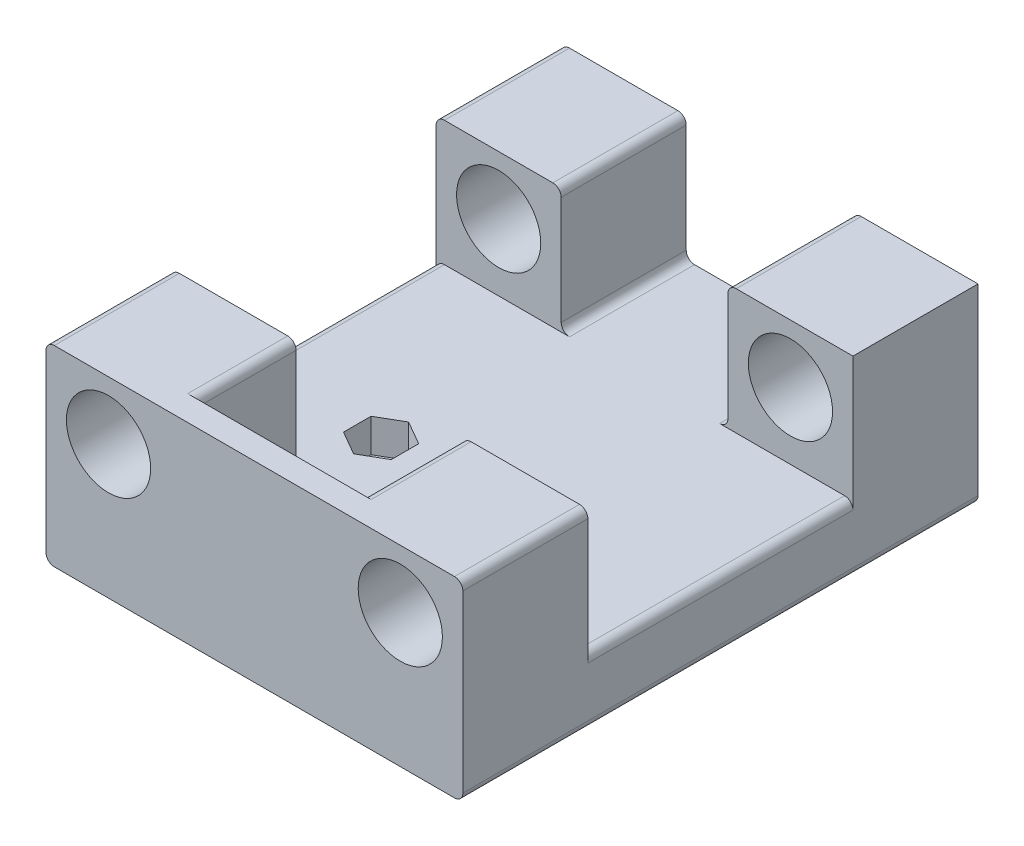
SolidWorks part; units mm, degrees
ref_plane "Front Plane" through (0, 0, 0) normal (0, 0, 1) x (1, 0, 0)
ref_plane "Top Plane" through (0, 0, 0) normal (0, 1, 0) x (1, 0, 0)
ref_plane "Right Plane" through (0, 0, 0) normal (1, 0, 0) x (0, 0, -1)
sketch "Sketch1" plane through (0, 0, 0) normal (0, 1, 0) x (1, 0, 0)
  line L1 (25, 30.9) -> (-25, 30.9)
  line L2 (25, 30.9) -> (25, -30.9)
  line L3 (25, -30.9) -> (-25, -30.9)
  line L4 (-25, 30.9) -> (-25, -30.9)
  line L5 (25, 30.9) -> (-25, -30.9) construction
  line L6 (25, -30.9) -> (-25, 30.9) construction
  point P0 (0, 0)
  dimension "D1" = 50
  dimension "D2" = 61.8
extrude "Boss-Extrude1" add sketch "Sketch1" along normal blind 5
sketch "Sketch2" plane through (0, 5, 0) normal (0, 1, 0) x (1, 0, 0)
  line L0 (-25, 30.9) -> (-25, -30.9) construction
  line L1 (-25, 30.9) -> (-10, 30.9)
  line L2 (-25, 30.9) -> (-25, 15.9)
  line L3 (-25, 15.9) -> (-10, 15.9)
  line L4 (-10, 30.9) -> (-10, 15.9)
  line L5 (25, -30.9) -> (25, 30.9) construction
  line L6 (25, 30.9) -> (10, 30.9)
  line L7 (25, 30.9) -> (25, 15.9)
  line L8 (25, 15.9) -> (10, 15.9)
  line L9 (10, 30.9) -> (10, 15.9)
  line L10 (25, 30.9) -> (-25, 30.9) construction
  line L11 (-25, -15.9) -> (-10, -15.9)
  line L12 (-25, -15.9) -> (-25, -30.9)
  line L13 (-25, -30.9) -> (-10, -30.9)
  line L14 (-10, -15.9) -> (-10, -30.9)
  line L15 (25, -15.9) -> (10, -15.9)
  line L16 (25, -15.9) -> (25, -30.9)
  line L17 (25, -30.9) -> (10, -30.9)
  line L18 (10, -15.9) -> (10, -30.9)
  line L19 (-25, -30.9) -> (25, -30.9) construction
  dimension "D1" = 15
  dimension "D2" = 15
extrude "Boss-Extrude2" add sketch "Sketch2" along normal blind 15
sketch "Sketch3" plane through (0, 0, 30.9) normal (0, 0, 1) x (1, 0, 0)
  line L0 (-25, 13) -> (25, 13) construction
  line L2 (25, 20) -> (25, 0) construction
  line L3 (-25, 20) -> (-25, 0) construction
  line L4 (-10, 5) -> (10, 5) construction
  line L5 (-17.5, 20) -> (-17.5, 0) construction
  line L6 (-25, 20) -> (-10, 20) construction
  line L7 (-25, 0) -> (25, 0) construction
  line L8 (17.5, 20) -> (17.5, 0) construction
  line L9 (10, 20) -> (25, 20) construction
  circle A0 centre (-17.5, 13) radius 5.05
  circle A1 centre (17.5, 13) radius 5.05
  point P3 (0, 13)
  point P19 (-17.5, 13)
  point P20 (17.5, 13)
  dimension "D2" = 10.1
  dimension "D3" = 10.1
  dimension "D1" = 8
extrude "Cut-Extrude1" cut sketch "Sketch3" against normal through all both and the other way through all
sketch "Sketch4" plane through (0, 5, 0) normal (0, 1, 0) x (1, 0, 0)
  line L0 (10, -15.9) -> (10, -30.9) construction
  line L1 (-10, -30.9) -> (10, -30.9)
  line L2 (-10, -30.9) -> (-10, -27.9)
  line L3 (-10, -27.9) -> (10, -27.9)
  line L4 (10, -30.9) -> (10, -27.9)
  dimension "D1" = 3
extrude "Boss-Extrude3" add sketch "Sketch4" along normal up to surface (15 mm away) up to face at (-17.5, 20, 23.4)
sketch "Sketch6" plane through (0, 0, 0) normal (0, -1, 0) x (1, 0, 0)
  line L4 (-25, 30.9) -> (-25, -30.9)
  line L5 (-25, -30.9) -> (25, -30.9)
  line L6 (25, -30.9) -> (25, 30.9)
  line L7 (25, 30.9) -> (-25, 30.9)
  line L8 (-25, 30.9) -> (-25, -30.9)
  line L9 (-25, -30.9) -> (25, -30.9)
  line L10 (25, -30.9) -> (25, 30.9)
  line L11 (25, 30.9) -> (-25, 30.9)
  dimension "D1" = 0
extrude "Boss-Extrude5" add sketch "Sketch6" along normal blind 3
fillet "Fillet1" radius 1 15 edges at (10, 20, -23.4) (10, 5, -23.4) (-10, 20, -23.4) (-10, 5, -23.4) (-10, 5, 21.9) (10, 5, 21.9) (10, 20, 21.9) (25, 20, 23.4) (-10, 20, 21.9) (-25, 20, 23.4) (-25, 20, -23.4) (25, 5, 0) (-25, 5, 0) (25, -3, 0) (-25, -3, 0)
sketch "Sketch7" plane through (0, 5, 0) normal (0, 1, 0) x (1, 0, 0)
  line L0 (-25, -5.9) -> (25, -5.9) construction
  line L1 (-25, -30.9) -> (-25, -15.9) construction
  line L2 (25, -15.9) -> (25, -30.9) construction
  line L3 (-9.8, -5.9) -> (9.8, -5.9) construction
  line L4 (-9, -15.9) -> (-9, -27.9) construction
  line L5 (-12.6579, -4.25) -> (-12.6579, -7.55)
  line L6 (-12.6579, -7.55) -> (-9.8, -9.2)
  line L7 (-9.8, -9.2) -> (-6.9421, -7.55)
  line L8 (-6.9421, -7.55) -> (-6.9421, -4.25)
  line L9 (-6.9421, -4.25) -> (-9.8, -2.6)
  line L10 (-9.8, -2.6) -> (-12.6579, -4.25)
  line L11 (-24, -30.9) -> (24, -30.9) construction
  line L12 (12.6579, -7.55) -> (12.6579, -4.25)
  line L13 (12.6579, -4.25) -> (9.8, -2.6)
  line L14 (9.8, -2.6) -> (6.9421, -4.25)
  line L15 (6.9421, -4.25) -> (6.9421, -7.55)
  line L16 (6.9421, -7.55) -> (9.8, -9.2)
  line L17 (9.8, -9.2) -> (12.6579, -7.55)
  line L18 (-9.8, -5.9) -> (9.8, -5.9) construction
  circle A0 centre (-9.8, -5.9) radius 2.8579 construction
  circle A1 centre (9.8, -5.9) radius 2.8579 construction
  point P9 (0, -5.9)
  point P27 (9.3, -9.2)
  point P29 (0, -5.9)
  dimension "D1" = 3.3
  dimension "D2" = 25
  dimension "D3" = 19.6
extrude "Cut-Extrude2" cut sketch "Sketch7" against normal blind 4
sketch "Sketch8" plane through (0, 1, 0) normal (0, 1, 0) x (1, 0, 0)
  line L0 (-9.8, -2.6) -> (-9.8, -9.2) construction
  line L1 (-12.6579, -5.9) -> (-6.9421, -5.9) construction
  line L2 (-12.6579, -4.25) -> (-12.6579, -7.55) construction
  line L3 (-6.9421, -7.55) -> (-6.9421, -4.25) construction
  line L4 (9.8, -2.6) -> (9.8, -9.2) construction
  line L5 (6.9421, -5.9) -> (12.6579, -5.9) construction
  line L7 (6.9421, -4.25) -> (6.9421, -7.55) construction
  line L8 (12.6579, -7.55) -> (12.6579, -4.25) construction
  point P19 (-9.8, -5.9)
  point P20 (9.8, -5.9)
  point P21 (6.1421, -5.9)
hole_wizard "M3 Clearance Hole1" positions "Sketch9" profile "Sketch10" hole size "M3" standard "ANSI Metric" end condition through all
sketch "Sketch9" plane through (0, 5, 0) normal (0, 1, 0) x (1, 0, 0)
  point P0 (-9.8, -5.9)
  point P3 (9.8, -5.9)
sketch "Sketch10" plane through (-9.8, 5, 5.9) normal (1, 0, 0) x (0, 0, 1)
  line L0 (0, 0) -> (0, 8)
  line L1 (0, 8) -> (1.7, 8)
  line L2 (1.7, 8) -> (1.7, 0)
  line L5 (1.7, 0) -> (0, 0)
  line L11 (0, -6.35) -> (0, 107.95) construction
  dimension "Thru Hole Dia." = 3.4
  dimension "Thru Hole Depth" = 8
